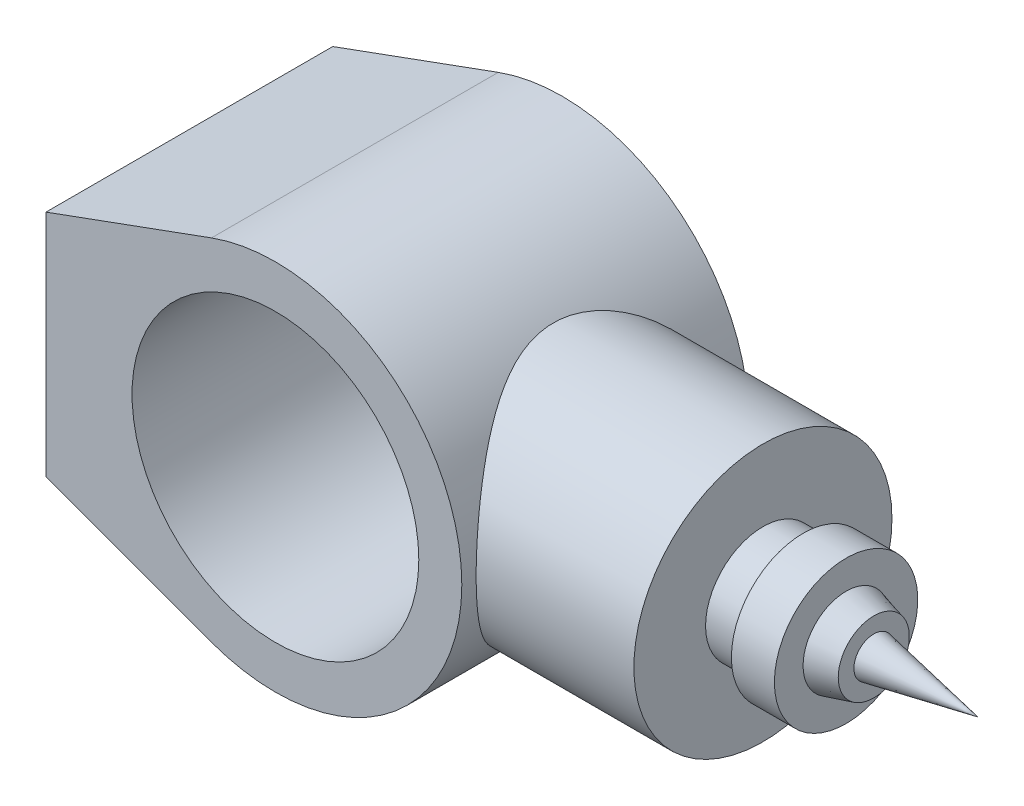
SolidWorks part; units mm, degrees
ref_plane "Front Plane" through (0, 0, 0) normal (0, 0, 1) x (1, 0, 0)
ref_plane "Top Plane" through (0, 0, 0) normal (0, 1, 0) x (1, 0, 0)
ref_plane "Right Plane" through (0, 0, 0) normal (1, 0, 0) x (0, 0, -1)
sketch "Sketch1" plane through (0, 0, 0) normal (0, 0, 1) x (1, 0, 0)
  line L0 (-80, -40) -> (-80, 40)
  line L1 (-80, 40) -> (-22.2817, 61.0617)
  line L2 (-80, -40) -> (-22.2817, -61.0617)
  arc A0 (-22.2817, -61.0617) -> (-22.2817, 61.0617) centre (0, 0) ccw
  circle A1 centre (0, 0) radius 50
  point P7 (-80, 0)
  dimension "D1" = 130
  dimension "D2" = 100
  dimension "D3" = 80
  dimension "D4" = 80
extrude "Boss-Extrude1" add sketch "Sketch1" along normal mid plane 100
ref_plane "Plane2" through (120, 0, 0) normal (1, 0, 0) x (0, 0, -1)
sketch "Sketch2" plane through (120, 0, 0) normal (1, 0, 0) x (0, 0, -1)
  circle A0 centre (0, 0) radius 45
  dimension "D1" = 90
extrude "Boss-Extrude2" add sketch "Sketch2" against normal up to next contours A0
sketch "Sketch4" plane through (0, 0, 0) normal (0, 0, 1) x (1, 0, 0)
  line L0 (0, 0) -> (233.1103, 0) construction
  line L1 (120, 0) -> (120, -20)
  line L2 (120, -45) -> (120, 45) construction
  line L3 (120, -20) -> (134, -20)
  line L4 (134, -20) -> (134, -25)
  line L5 (134, -25) -> (149, -25)
  line L6 (149, -25) -> (149, -15)
  line L7 (149, -15) -> (158.6536, -12.3909)
  line L8 (158.6536, -12.3909) -> (158.6536, -6.924)
  line L9 (158.6536, -6.924) -> (195, 0)
  line L10 (195, 0) -> (120, 0)
  dimension "D1" = 20
  dimension "D2" = 14
  dimension "D3" = 5
  dimension "D4" = 15
  dimension "D5" = 10
  dimension "D6" = 10
  dimension "D7" = 37
  dimension "D8" = 75
revolve "Revolve1" add sketch "Sketch4" angle 360 about L0
